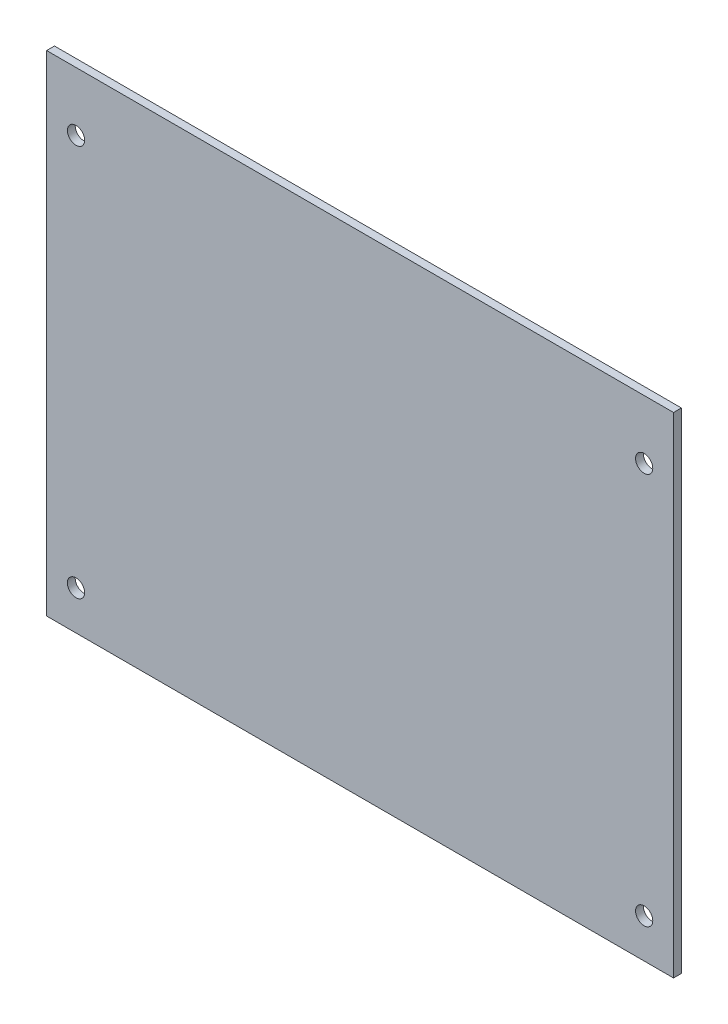
SolidWorks part; units mm, degrees
ref_plane "正面" through (0, 0, 0) normal (0, 0, 1) x (1, 0, 0)
ref_plane "平面" through (0, 0, 0) normal (0, 1, 0) x (1, 0, 0)
ref_plane "右側面" through (0, 0, 0) normal (1, 0, 0) x (0, 0, -1)
sketch "ｽｹｯﾁ1" plane through (0, 0, 0) normal (0, 0, 1) x (1, 0, 0)
  line L1 (-80, 62.5) -> (80, 62.5)
  line L2 (-80, 62.5) -> (-80, -62.5)
  line L3 (-80, -62.5) -> (80, -62.5)
  line L4 (80, 62.5) -> (80, -62.5)
  line L5 (-80, 62.5) -> (80, -62.5) construction
  line L6 (-80, -62.5) -> (80, 62.5) construction
  point P0 (0, 0)
  dimension "D1" = 125
  dimension "D2" = 160
extrude "ﾎﾞｽ - 押し出し1" add sketch "ｽｹｯﾁ1" along normal blind 2
sketch "ｽｹｯﾁ2" plane through (0, 0, 2) normal (0, 0, 1) x (1, 0, 0)
  line L0 (80, -62.5) -> (72.5, -62.5)
  line L1 (-80, -62.5) -> (80, -62.5) construction
  line L2 (72.5, -62.5) -> (72.5, -52.5)
  line L3 (-80, -62.5) -> (-72.5, -62.5)
  line L4 (-72.5, -62.5) -> (-72.5, -52.5)
  line L5 (-72.5, -52.5) -> (-72.5, 47.5)
  line L6 (72.5, -52.5) -> (72.5, 47.5)
  circle A0 centre (72.5, -52.5) radius 2.2
  circle A1 centre (-72.5, -52.5) radius 2.2
  circle A2 centre (-72.5, 47.5) radius 2.2
  circle A3 centre (72.5, 47.5) radius 2.2
  dimension "D5" = 4.4
  dimension "D6" = 4.4
  dimension "D9" = 4.4
  dimension "D10" = 4.4
  dimension "D1" = 7.5
  dimension "D2" = 7.5
  dimension "D3" = 10
  dimension "D4" = 10
  dimension "D7" = 100
  dimension "D8" = 100
extrude "ｶｯﾄ - 押し出し1" cut sketch "ｽｹｯﾁ2" against normal blind 2
